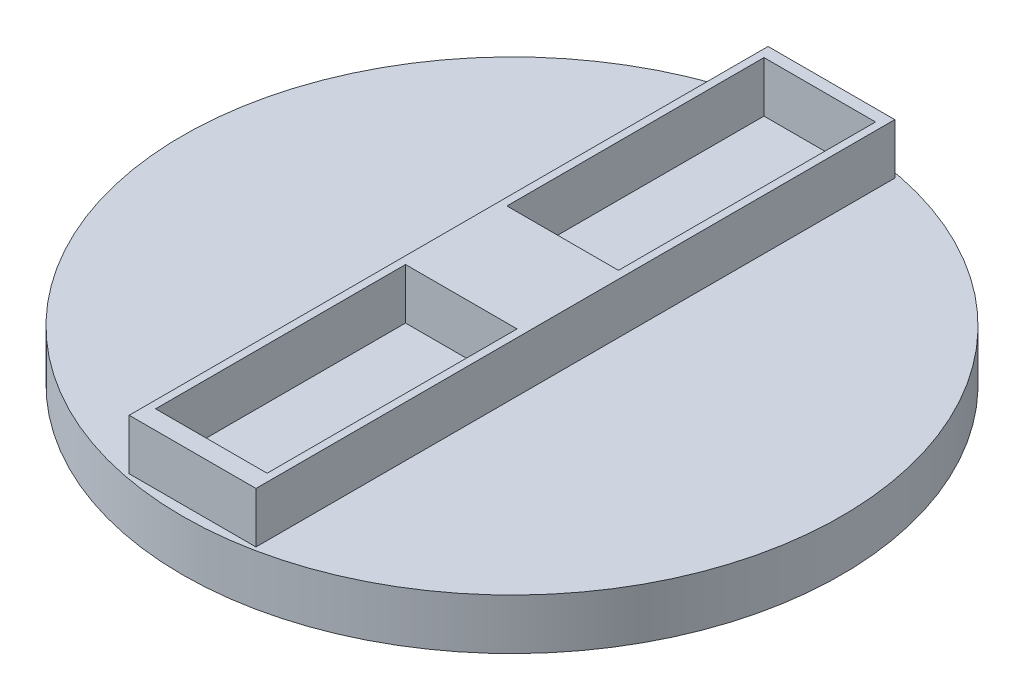
SolidWorks part; units mm, degrees
ref_plane "Front Plane" through (0, 0, 0) normal (0, 0, 1) x (1, 0, 0)
ref_plane "Top Plane" through (0, 0, 0) normal (0, 1, 0) x (1, 0, 0)
ref_plane "Right Plane" through (0, 0, 0) normal (1, 0, 0) x (0, 0, -1)
sketch "Sketch1" plane through (0, 0, 0) normal (0, 1, 0) x (1, 0, 0)
  line L0 (-11, 10) -> (11, 10)
  line L1 (-12.5, -63) -> (12.5, -63)
  line L2 (-12.5, -63) -> (-12.5, 63)
  line L3 (-12.5, 63) -> (12.5, 63)
  line L4 (12.5, -63) -> (12.5, 63)
  line L5 (-11, -59.3019) -> (11, -59.3019)
  line L6 (-11, -59.3019) -> (-11, -10)
  line L7 (-11, 60.6981) -> (11, 60.6981)
  line L8 (11, -59.3019) -> (11, -10)
  line L9 (-11, -10) -> (11, -10)
  line L10 (-11, 10) -> (-11, 60.6981)
  line L11 (11, 10) -> (11, 60.6981)
  point P0 (0, 0)
  point P6 (0, 0)
  dimension "D1" = 126
  dimension "D2" = 25
  dimension "D3" = 120
  dimension "D4" = 20
  dimension "D5" = 10
  dimension "D6" = 22
  dimension "D7" = 1.5
  dimension "D8" = 12.5
extrude "Boss-Extrude1" add sketch "Sketch1" along normal blind 10
sketch "Sketch2" plane through (0, 0, 0) normal (0, 1, 0) x (1, 0, 0)
  circle A0 centre (0, 0) radius 65
  point P0 (0, 0)
extrude "Boss-Extrude2" add sketch "Sketch2" against normal blind 10
